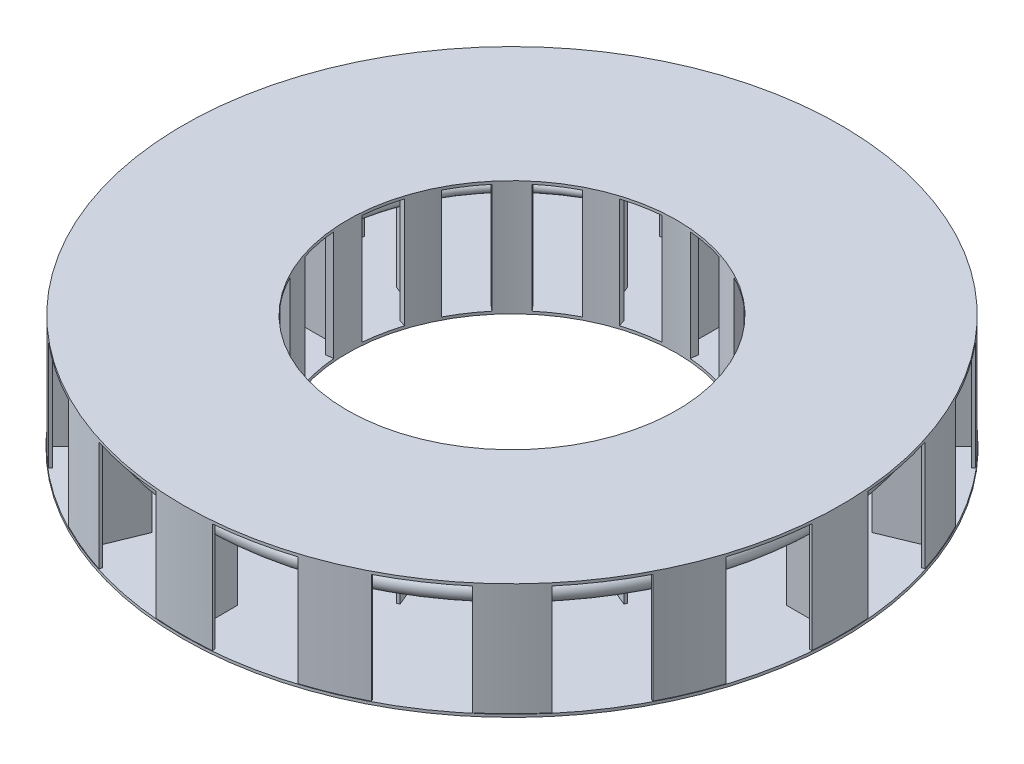
SolidWorks part; units mm, degrees
material "AISI 1035 Steel (SS)"
ref_plane "Front Plane" through (0, 0, 0) normal (0, 0, 1) x (1, 0, 0)
ref_plane "Top Plane" through (0, 0, 0) normal (0, 1, 0) x (1, 0, 0)
ref_plane "Right Plane" through (0, 0, 0) normal (1, 0, 0) x (0, 0, -1)
ref_plane "Plane1" through (0, 2500, 0) normal (0, 1, 0) x (1, 0, 0)
sketch "Sketch1" plane through (0, 0, 0) normal (0, 1, 0) x (1, 0, 0)
  line L0 (0, 0) -> (-6.0848, 0) construction
  line L1 (-6.0848, 0) -> (0, 5.9086) construction
  line L2 (0, 5.9086) -> (0, 0) construction
  line L3 (-6.0848, 0) -> (0, 4500) construction
  line L4 (0, 9000) -> (0, 4500) construction
  line L5 (0, 0) -> (9000, 0) construction
  line L6 (0, 0) -> (0, -9000) construction
  line L7 (0, 5.9086) -> (-9000, 0) construction
  circle A0 centre (0, 0) radius 9000
  circle A1 centre (0, 0) radius 4500
  dimension "D1" = 18000
  dimension "D2" = 9000
extrude "Boss-Extrude1" add sketch "Sketch1" along normal blind 75
sketch "Sketch2" plane through (0, 75, 0) normal (0, 1, 0) x (1, 0, 0)
  line L0 (0, 0) -> (0, 9000) construction
  line L1 (-387.6109, 4483.2753) -> (-405.0458, 4682.5141)
  line L2 (1357.5694, 4290.3386) -> (1417.707, 4481.0832)
  line L3 (3368.52, 8248.1415) -> (2850.1429, 6978.8457)
  line L4 (2850.1429, 6978.8457) -> (2919.4338, 6950.1445)
  line L5 (2919.4338, 6950.1445) -> (3444.1242, 8216.8591)
  line L6 (1763.9094, 4356.4462) -> (2161.3127, 5315.8626)
  line L7 (2161.3127, 5315.8626) -> (2230.6036, 5287.1613)
  line L8 (1833.2004, 4327.745) -> (2230.6036, 5287.1613)
  line L9 (2691.9077, 8493.0794) -> (2714.5682, 8564.5742)
  line L10 (4132.8154, 7977.5089) -> (4098.3158, 7910.9148)
  line L11 (2073.781, 3993.674) -> (2166.1341, 4171.0746)
  line L12 (2896.0721, 3444.2367) -> (3024.6268, 3597.4481)
  line L13 (6268.5338, 6331.2123) -> (5303.8773, 5356.9103)
  line L14 (5303.8773, 5356.9103) -> (5356.9103, 5303.8773)
  line L15 (5356.9103, 5303.8773) -> (6326.4117, 6273.3787)
  line L16 (3296.7796, 3349.8126) -> (4031.0851, 4084.1181)
  line L17 (4031.0851, 4084.1181) -> (4084.1181, 4031.0851)
  line L18 (3349.8126, 3296.7796) -> (4084.1181, 4031.0851)
  line L19 (5737.1592, 6816.4338) -> (5785.4546, 6873.8146)
  line L20 (6871.0841, 5788.6972) -> (6813.7261, 5740.3747)
  line L21 (-44.3204, 8909.3659) -> (-37.5, 7538.3152)
  line L22 (-37.5, 7538.3152) -> (37.5, 7538.3152)
  line L23 (37.5, 7538.3152) -> (37.5, 8909.3972)
  line L26 (-37.5, 4699.8504) -> (-37.5, 5738.3152)
  line L27 (-37.5, 5738.3152) -> (37.5, 5738.3152)
  line L28 (37.5, 4699.8504) -> (37.5, 5738.3152)
  line L43 (3444.2367, 2896.0721) -> (3597.4481, 3024.6268)
  line L44 (3993.674, 2073.781) -> (4171.0746, 2166.1341)
  line L45 (8214.2201, 3450.4135) -> (6950.1445, 2919.4338)
  line L112 (6950.1445, 2919.4338) -> (6978.8457, 2850.1429)
  line L113 (6978.8457, 2850.1429) -> (8245.5604, 3374.8332)
  line L114 (4327.745, 1833.2004) -> (5287.1613, 2230.6036)
  line L136 (-763.1624, 8876.7307) -> (-769.5867, 8951.4551)
  line L143 (765.3631, 8951.8172) -> (758.974, 8877.0898)
  line L224 (5287.1613, 2230.6036) -> (5315.8626, 2161.3127)
  line L225 (387.6109, 4483.2753) -> (405.0458, 4682.5141)
  line L226 (4356.4462, 1763.9094) -> (5315.8626, 2161.3127)
  line L227 (7908.9802, 4102.0479) -> (7975.5581, 4136.5789)
  line L228 (8563.2925, 2718.6088) -> (8491.8084, 2695.9146)
  line L229 (4290.3386, 1357.5694) -> (4481.0832, 1417.707)
  line L230 (4483.2753, 387.6109) -> (4682.5141, 405.0458)
  line L231 (8909.3659, 44.3204) -> (7538.3152, 37.5)
  line L232 (7538.3152, 37.5) -> (7538.3152, -37.5)
  line L233 (7538.3152, -37.5) -> (8909.3972, -37.5)
  line L234 (4699.8504, 37.5) -> (5738.3152, 37.5)
  line L235 (5738.3152, 37.5) -> (5738.3152, -37.5)
  line L236 (4699.8504, -37.5) -> (5738.3152, -37.5)
  line L237 (8876.7307, 763.1624) -> (8951.4551, 769.5867)
  line L238 (8951.8172, -765.3631) -> (8877.0898, -758.974)
  line L239 (4483.2753, -387.6109) -> (4682.5141, -405.0458)
  line L240 (4290.3386, -1357.5694) -> (4481.0832, -1417.707)
  line L241 (8248.1415, -3368.52) -> (6978.8457, -2850.1429)
  line L242 (6978.8457, -2850.1429) -> (6950.1445, -2919.4338)
  line L243 (6950.1445, -2919.4338) -> (8216.8591, -3444.1242)
  line L244 (4356.4462, -1763.9094) -> (5315.8626, -2161.3127)
  line L245 (5315.8626, -2161.3127) -> (5287.1613, -2230.6036)
  line L246 (4327.745, -1833.2004) -> (5287.1613, -2230.6036)
  line L247 (8493.0794, -2691.9077) -> (8564.5742, -2714.5682)
  line L248 (7977.5089, -4132.8154) -> (7910.9148, -4098.3158)
  line L249 (3993.674, -2073.781) -> (4171.0746, -2166.1341)
  line L250 (3444.2367, -2896.0721) -> (3597.4481, -3024.6268)
  line L251 (6331.2123, -6268.5338) -> (5356.9103, -5303.8773)
  line L252 (5356.9103, -5303.8773) -> (5303.8773, -5356.9103)
  line L253 (5303.8773, -5356.9103) -> (6273.3787, -6326.4117)
  line L254 (3349.8126, -3296.7796) -> (4084.1181, -4031.0851)
  line L255 (4084.1181, -4031.0851) -> (4031.0851, -4084.1181)
  line L256 (3296.7796, -3349.8126) -> (4031.0851, -4084.1181)
  line L257 (6816.4338, -5737.1592) -> (6873.8146, -5785.4546)
  line L258 (5788.6972, -6871.0841) -> (5740.3747, -6813.7261)
  line L260 (2896.0721, -3444.2367) -> (3024.6268, -3597.4481)
  line L262 (2073.781, -3993.674) -> (2166.1341, -4171.0746)
  line L264 (3450.4135, -8214.2201) -> (2919.4338, -6950.1445)
  line L266 (2919.4338, -6950.1445) -> (2850.1429, -6978.8457)
  line L268 (2850.1429, -6978.8457) -> (3374.8332, -8245.5604)
  line L270 (1833.2004, -4327.745) -> (2230.6036, -5287.1613)
  line L272 (2230.6036, -5287.1613) -> (2161.3127, -5315.8626)
  line L273 (1763.9094, -4356.4462) -> (2161.3127, -5315.8626)
  line L274 (4102.0479, -7908.9802) -> (4136.5789, -7975.5581)
  line L275 (2718.6088, -8563.2925) -> (2695.9146, -8491.8084)
  line L276 (1357.5694, -4290.3386) -> (1417.707, -4481.0832)
  line L277 (387.6109, -4483.2753) -> (405.0458, -4682.5141)
  line L278 (44.3204, -8909.3659) -> (37.5, -7538.3152)
  line L279 (37.5, -7538.3152) -> (-37.5, -7538.3152)
  line L280 (-37.5, -7538.3152) -> (-37.5, -8909.3972)
  line L281 (37.5, -4699.8504) -> (37.5, -5738.3152)
  line L282 (37.5, -5738.3152) -> (-37.5, -5738.3152)
  line L283 (-37.5, -4699.8504) -> (-37.5, -5738.3152)
  line L284 (763.1624, -8876.7307) -> (769.5867, -8951.4551)
  line L285 (-765.3631, -8951.8172) -> (-758.974, -8877.0898)
  line L286 (-387.6109, -4483.2753) -> (-405.0458, -4682.5141)
  line L287 (-1357.5694, -4290.3386) -> (-1417.707, -4481.0832)
  line L288 (-3368.52, -8248.1415) -> (-2850.1429, -6978.8457)
  line L289 (-2850.1429, -6978.8457) -> (-2919.4338, -6950.1445)
  line L290 (-2919.4338, -6950.1445) -> (-3444.1242, -8216.8591)
  line L291 (-1763.9094, -4356.4462) -> (-2161.3127, -5315.8626)
  line L292 (-2161.3127, -5315.8626) -> (-2230.6036, -5287.1613)
  line L293 (-1833.2004, -4327.745) -> (-2230.6036, -5287.1613)
  line L294 (-2691.9077, -8493.0794) -> (-2714.5682, -8564.5742)
  line L295 (-4132.8154, -7977.5089) -> (-4098.3158, -7910.9148)
  line L296 (-2073.781, -3993.674) -> (-2166.1341, -4171.0746)
  line L297 (-2896.0721, -3444.2367) -> (-3024.6268, -3597.4481)
  line L298 (-6268.5338, -6331.2123) -> (-5303.8773, -5356.9103)
  line L299 (-5303.8773, -5356.9103) -> (-5356.9103, -5303.8773)
  line L300 (-5356.9103, -5303.8773) -> (-6326.4117, -6273.3787)
  line L301 (-3296.7796, -3349.8126) -> (-4031.0851, -4084.1181)
  line L303 (-4031.0851, -4084.1181) -> (-4084.1181, -4031.0851)
  line L305 (-3349.8126, -3296.7796) -> (-4084.1181, -4031.0851)
  line L307 (-5737.1592, -6816.4338) -> (-5785.4546, -6873.8146)
  line L310 (-6871.0841, -5788.6972) -> (-6813.7261, -5740.3747)
  line L311 (-3444.2367, -2896.0721) -> (-3597.4481, -3024.6268)
  line L312 (-3993.674, -2073.781) -> (-4171.0746, -2166.1341)
  line L313 (-8214.2201, -3450.4135) -> (-6950.1445, -2919.4338)
  line L314 (-6950.1445, -2919.4338) -> (-6978.8457, -2850.1429)
  line L315 (-6978.8457, -2850.1429) -> (-8245.5604, -3374.8332)
  line L316 (-4327.745, -1833.2004) -> (-5287.1613, -2230.6036)
  line L317 (-5287.1613, -2230.6036) -> (-5315.8626, -2161.3127)
  line L318 (-4356.4462, -1763.9094) -> (-5315.8626, -2161.3127)
  line L319 (-7908.9802, -4102.0479) -> (-7975.5581, -4136.5789)
  line L320 (-8563.2925, -2718.6088) -> (-8491.8084, -2695.9146)
  line L321 (-4290.3386, -1357.5694) -> (-4481.0832, -1417.707)
  line L322 (-4483.2753, -387.6109) -> (-4682.5141, -405.0458)
  line L323 (-8909.3659, -44.3204) -> (-7538.3152, -37.5)
  line L324 (-7538.3152, -37.5) -> (-7538.3152, 37.5)
  line L325 (-7538.3152, 37.5) -> (-8909.3972, 37.5)
  line L326 (-4699.8504, -37.5) -> (-5738.3152, -37.5)
  line L327 (-5738.3152, -37.5) -> (-5738.3152, 37.5)
  line L328 (-4699.8504, 37.5) -> (-5738.3152, 37.5)
  line L329 (-8876.7307, -763.1624) -> (-8951.4551, -769.5867)
  line L330 (-8951.8172, 765.3631) -> (-8877.0898, 758.974)
  line L331 (-4483.2753, 387.6109) -> (-4682.5141, 405.0458)
  line L332 (-4290.3386, 1357.5694) -> (-4481.0832, 1417.707)
  line L333 (-8248.1415, 3368.52) -> (-6978.8457, 2850.1429)
  line L334 (-6978.8457, 2850.1429) -> (-6950.1445, 2919.4338)
  line L335 (-6950.1445, 2919.4338) -> (-8216.8591, 3444.1242)
  line L337 (-4356.4462, 1763.9094) -> (-5315.8626, 2161.3127)
  line L339 (-5315.8626, 2161.3127) -> (-5287.1613, 2230.6036)
  line L340 (-4327.745, 1833.2004) -> (-5287.1613, 2230.6036)
  line L341 (-8493.0794, 2691.9077) -> (-8564.5742, 2714.5682)
  line L342 (-7977.5089, 4132.8154) -> (-7910.9148, 4098.3158)
  line L343 (-3993.674, 2073.781) -> (-4171.0746, 2166.1341)
  line L344 (-3444.2367, 2896.0721) -> (-3597.4481, 3024.6268)
  line L345 (-6331.2123, 6268.5338) -> (-5356.9103, 5303.8773)
  line L346 (-5356.9103, 5303.8773) -> (-5303.8773, 5356.9103)
  line L347 (-5303.8773, 5356.9103) -> (-6273.3787, 6326.4117)
  line L348 (-3349.8126, 3296.7796) -> (-4084.1181, 4031.0851)
  line L349 (-4084.1181, 4031.0851) -> (-4031.0851, 4084.1181)
  line L350 (-3296.7796, 3349.8126) -> (-4031.0851, 4084.1181)
  line L351 (-6816.4338, 5737.1592) -> (-6873.8146, 5785.4546)
  line L352 (-5788.6972, 6871.0841) -> (-5740.3747, 6813.7261)
  line L353 (-2896.0721, 3444.2367) -> (-3024.6268, 3597.4481)
  line L355 (-2073.781, 3993.674) -> (-2166.1341, 4171.0746)
  line L357 (-3450.4135, 8214.2201) -> (-2919.4338, 6950.1445)
  line L358 (-2919.4338, 6950.1445) -> (-2850.1429, 6978.8457)
  line L359 (-2850.1429, 6978.8457) -> (-3374.8332, 8245.5604)
  line L360 (-1833.2004, 4327.745) -> (-2230.6036, 5287.1613)
  line L361 (-2230.6036, 5287.1613) -> (-2161.3127, 5315.8626)
  line L362 (-1763.9094, 4356.4462) -> (-2161.3127, 5315.8626)
  line L363 (-4102.0479, 7908.9802) -> (-4136.5789, 7975.5581)
  line L364 (-2718.6088, 8563.2925) -> (-2695.9146, 8491.8084)
  line L365 (-1357.5694, 4290.3386) -> (-1417.707, 4481.0832)
  circle A0 centre (0, 0) radius 9000 construction
  arc A5 (765.3631, 8951.8172) -> (-769.5867, 8951.4551) centre (0, 0) ccw
  arc A6 (758.974, 8877.0898) -> (37.5, 8909.3972) centre (0, 0) ccw
  arc A51 (-44.3204, 8909.3659) -> (-763.1624, 8876.7307) centre (0, 0) ccw
  arc A72 (387.6109, 4483.2753) -> (-387.6109, 4483.2753) centre (0, 0) ccw
  circle A73 centre (0, 0) radius 4500 construction
  arc A74 (405.0458, 4682.5141) -> (37.5, 4699.8504) centre (0, 0) ccw
  arc A75 (-405.0458, 4682.5141) -> (-37.5, 4699.8504) centre (0, 0) cw
  arc A76 (4132.8154, 7977.5089) -> (2714.5682, 8564.5742) centre (0, 0) ccw
  arc A77 (4098.3158, 7910.9148) -> (3444.1242, 8216.8591) centre (0, 0) ccw
  arc A78 (3368.52, 8248.1415) -> (2691.9077, 8493.0794) centre (0, 0) ccw
  arc A79 (2073.781, 3993.674) -> (1357.5694, 4290.3386) centre (0, 0) ccw
  arc A80 (2166.1341, 4171.0746) -> (1833.2004, 4327.745) centre (0, 0) ccw
  arc A81 (1417.707, 4481.0832) -> (1763.9094, 4356.4462) centre (0, 0) cw
  arc A82 (6871.0841, 5788.6972) -> (5785.4546, 6873.8146) centre (0, 0) ccw
  arc A83 (6813.7261, 5740.3747) -> (6326.4117, 6273.3787) centre (0, 0) ccw
  arc A84 (6268.5338, 6331.2123) -> (5737.1592, 6816.4338) centre (0, 0) ccw
  arc A85 (3444.2367, 2896.0721) -> (2896.0721, 3444.2367) centre (0, 0) ccw
  arc A86 (3597.4481, 3024.6268) -> (3349.8126, 3296.7796) centre (0, 0) ccw
  arc A87 (3024.6268, 3597.4481) -> (3296.7796, 3349.8126) centre (0, 0) cw
  arc A88 (8563.2925, 2718.6088) -> (7975.5581, 4136.5789) centre (0, 0) ccw
  arc A89 (8491.8084, 2695.9146) -> (8245.5604, 3374.8332) centre (0, 0) ccw
  arc A90 (8214.2201, 3450.4135) -> (7908.9802, 4102.0479) centre (0, 0) ccw
  arc A91 (4290.3386, 1357.5694) -> (3993.674, 2073.781) centre (0, 0) ccw
  arc A92 (4481.0832, 1417.707) -> (4356.4462, 1763.9094) centre (0, 0) ccw
  arc A93 (4171.0746, 2166.1341) -> (4327.745, 1833.2004) centre (0, 0) cw
  arc A94 (8951.8172, -765.3631) -> (8951.4551, 769.5867) centre (0, 0) ccw
  arc A95 (8877.0898, -758.974) -> (8909.3972, -37.5) centre (0, 0) ccw
  arc A96 (8909.3659, 44.3204) -> (8876.7307, 763.1624) centre (0, 0) ccw
  arc A97 (4483.2753, -387.6109) -> (4483.2753, 387.6109) centre (0, 0) ccw
  arc A98 (4682.5141, -405.0458) -> (4699.8504, -37.5) centre (0, 0) ccw
  arc A99 (4682.5141, 405.0458) -> (4699.8504, 37.5) centre (0, 0) cw
  arc A100 (7977.5089, -4132.8154) -> (8564.5742, -2714.5682) centre (0, 0) ccw
  arc A101 (7910.9148, -4098.3158) -> (8216.8591, -3444.1242) centre (0, 0) ccw
  arc A102 (8248.1415, -3368.52) -> (8493.0794, -2691.9077) centre (0, 0) ccw
  arc A103 (3993.674, -2073.781) -> (4290.3386, -1357.5694) centre (0, 0) ccw
  arc A104 (4171.0746, -2166.1341) -> (4327.745, -1833.2004) centre (0, 0) ccw
  arc A105 (4481.0832, -1417.707) -> (4356.4462, -1763.9094) centre (0, 0) cw
  arc A106 (5788.6972, -6871.0841) -> (6873.8146, -5785.4546) centre (0, 0) ccw
  arc A107 (5740.3747, -6813.7261) -> (6273.3787, -6326.4117) centre (0, 0) ccw
  arc A108 (6331.2123, -6268.5338) -> (6816.4338, -5737.1592) centre (0, 0) ccw
  arc A109 (2896.0721, -3444.2367) -> (3444.2367, -2896.0721) centre (0, 0) ccw
  arc A110 (3024.6268, -3597.4481) -> (3296.7796, -3349.8126) centre (0, 0) ccw
  arc A111 (3597.4481, -3024.6268) -> (3349.8126, -3296.7796) centre (0, 0) cw
  arc A112 (2718.6088, -8563.2925) -> (4136.5789, -7975.5581) centre (0, 0) ccw
  arc A113 (2695.9146, -8491.8084) -> (3374.8332, -8245.5604) centre (0, 0) ccw
  arc A114 (3450.4135, -8214.2201) -> (4102.0479, -7908.9802) centre (0, 0) ccw
  arc A115 (1357.5694, -4290.3386) -> (2073.781, -3993.674) centre (0, 0) ccw
  arc A116 (1417.707, -4481.0832) -> (1763.9094, -4356.4462) centre (0, 0) ccw
  arc A117 (2166.1341, -4171.0746) -> (1833.2004, -4327.745) centre (0, 0) cw
  arc A118 (-765.3631, -8951.8172) -> (769.5867, -8951.4551) centre (0, 0) ccw
  arc A119 (-758.974, -8877.0898) -> (-37.5, -8909.3972) centre (0, 0) ccw
  arc A120 (44.3204, -8909.3659) -> (763.1624, -8876.7307) centre (0, 0) ccw
  arc A121 (-387.6109, -4483.2753) -> (387.6109, -4483.2753) centre (0, 0) ccw
  arc A122 (-405.0458, -4682.5141) -> (-37.5, -4699.8504) centre (0, 0) ccw
  arc A123 (405.0458, -4682.5141) -> (37.5, -4699.8504) centre (0, 0) cw
  arc A124 (-4132.8154, -7977.5089) -> (-2714.5682, -8564.5742) centre (0, 0) ccw
  arc A125 (-4098.3158, -7910.9148) -> (-3444.1242, -8216.8591) centre (0, 0) ccw
  arc A126 (-3368.52, -8248.1415) -> (-2691.9077, -8493.0794) centre (0, 0) ccw
  arc A127 (-2073.781, -3993.674) -> (-1357.5694, -4290.3386) centre (0, 0) ccw
  arc A128 (-2166.1341, -4171.0746) -> (-1833.2004, -4327.745) centre (0, 0) ccw
  arc A129 (-1417.707, -4481.0832) -> (-1763.9094, -4356.4462) centre (0, 0) cw
  arc A130 (-6871.0841, -5788.6972) -> (-5785.4546, -6873.8146) centre (0, 0) ccw
  arc A131 (-6813.7261, -5740.3747) -> (-6326.4117, -6273.3787) centre (0, 0) ccw
  arc A132 (-6268.5338, -6331.2123) -> (-5737.1592, -6816.4338) centre (0, 0) ccw
  arc A133 (-3444.2367, -2896.0721) -> (-2896.0721, -3444.2367) centre (0, 0) ccw
  arc A134 (-3597.4481, -3024.6268) -> (-3349.8126, -3296.7796) centre (0, 0) ccw
  arc A135 (-3024.6268, -3597.4481) -> (-3296.7796, -3349.8126) centre (0, 0) cw
  arc A136 (-8563.2925, -2718.6088) -> (-7975.5581, -4136.5789) centre (0, 0) ccw
  arc A137 (-8491.8084, -2695.9146) -> (-8245.5604, -3374.8332) centre (0, 0) ccw
  arc A138 (-8214.2201, -3450.4135) -> (-7908.9802, -4102.0479) centre (0, 0) ccw
  arc A139 (-4290.3386, -1357.5694) -> (-3993.674, -2073.781) centre (0, 0) ccw
  arc A140 (-4481.0832, -1417.707) -> (-4356.4462, -1763.9094) centre (0, 0) ccw
  arc A141 (-4171.0746, -2166.1341) -> (-4327.745, -1833.2004) centre (0, 0) cw
  arc A142 (-8951.8172, 765.3631) -> (-8951.4551, -769.5867) centre (0, 0) ccw
  arc A143 (-8877.0898, 758.974) -> (-8909.3972, 37.5) centre (0, 0) ccw
  arc A144 (-8909.3659, -44.3204) -> (-8876.7307, -763.1624) centre (0, 0) ccw
  arc A145 (-4483.2753, 387.6109) -> (-4483.2753, -387.6109) centre (0, 0) ccw
  arc A146 (-4682.5141, 405.0458) -> (-4699.8504, 37.5) centre (0, 0) ccw
  arc A147 (-4682.5141, -405.0458) -> (-4699.8504, -37.5) centre (0, 0) cw
  arc A148 (-7977.5089, 4132.8154) -> (-8564.5742, 2714.5682) centre (0, 0) ccw
  arc A149 (-7910.9148, 4098.3158) -> (-8216.8591, 3444.1242) centre (0, 0) ccw
  arc A150 (-8248.1415, 3368.52) -> (-8493.0794, 2691.9077) centre (0, 0) ccw
  arc A151 (-3993.674, 2073.781) -> (-4290.3386, 1357.5694) centre (0, 0) ccw
  arc A152 (-4171.0746, 2166.1341) -> (-4327.745, 1833.2004) centre (0, 0) ccw
  arc A153 (-4481.0832, 1417.707) -> (-4356.4462, 1763.9094) centre (0, 0) cw
  arc A154 (-5788.6972, 6871.0841) -> (-6873.8146, 5785.4546) centre (0, 0) ccw
  arc A155 (-5740.3747, 6813.7261) -> (-6273.3787, 6326.4117) centre (0, 0) ccw
  arc A156 (-6331.2123, 6268.5338) -> (-6816.4338, 5737.1592) centre (0, 0) ccw
  arc A157 (-2896.0721, 3444.2367) -> (-3444.2367, 2896.0721) centre (0, 0) ccw
  arc A158 (-3024.6268, 3597.4481) -> (-3296.7796, 3349.8126) centre (0, 0) ccw
  arc A159 (-3597.4481, 3024.6268) -> (-3349.8126, 3296.7796) centre (0, 0) cw
  arc A160 (-2718.6088, 8563.2925) -> (-4136.5789, 7975.5581) centre (0, 0) ccw
  arc A161 (-2695.9146, 8491.8084) -> (-3374.8332, 8245.5604) centre (0, 0) ccw
  arc A162 (-3450.4135, 8214.2201) -> (-4102.0479, 7908.9802) centre (0, 0) ccw
  arc A163 (-1357.5694, 4290.3386) -> (-2073.781, 3993.674) centre (0, 0) ccw
  arc A164 (-1417.707, 4481.0832) -> (-1763.9094, 4356.4462) centre (0, 0) ccw
  arc A165 (-2166.1341, 4171.0746) -> (-1833.2004, 4327.745) centre (0, 0) cw
  point P3 (25, 7538.3152)
  point P30 (0, 0)
  point P31 (0, 7538.3152)
  point P34 (0, 5738.3152)
  point P177 (0, 0)
  point P268 (0, 0)
  point P270 (0, 0)
  dimension "D1" = 16
  dimension "D2" = 200
  dimension "D3" = 75
  dimension "D4" = 9000
  dimension "D6" = 1800
  dimension "D8" = 75
extrude "Boss-Extrude5" add sketch "Sketch2" along normal blind 3000
sketch "Sketch4" plane through (0, 0, 0) normal (1, 0, 0) x (0, 0, -1)
  line L0 (9900, 2500) -> (-9900, 2500) construction
  line L1 (-5287.1613, 3075) -> (-5287.1613, 75) construction
  circle A0 centre (-5287.1613, 2500) radius 150
  circle A1 centre (-8243.086, 2500) radius 250
  point P4 (-7847.7085, 2500)
  point P7 (-4536.4219, 2500)
  point P10 (-8243.086, 2500)
  point P11 (-5291.9449, 2500)
  dimension "D1" = 500
  dimension "D2" = 300
sketch "Sketch5" plane through (0, 2500, 0) normal (0, 1, 0) x (1, 0, 0)
  line L0 (-44.3204, 8909.3659) -> (-37.5, 7538.3152) construction
  line L1 (-2850.1429, 6978.8457) -> (-3374.8332, 8245.5604) construction
  arc A1 (-3119.8143, 7629.8902) -> (-41.0054, 8242.984) centre (0, 0) ccw
  point P1 (-28.3491, 7847.6573)
  point P6 (-2980.0758, 7259.8675)
sweep "Sweep3" add profiles "Sketch4" path "Sketch5"
sketch "Sketch7" plane through (0, 3075, 0) normal (0, 1, 0) x (1, 0, 0)
  circle A0 centre (0, 0) radius 4500
  circle A1 centre (0, 0) radius 8984.4762
extrude "Boss-Extrude6" add sketch "Sketch7" along normal blind 75
